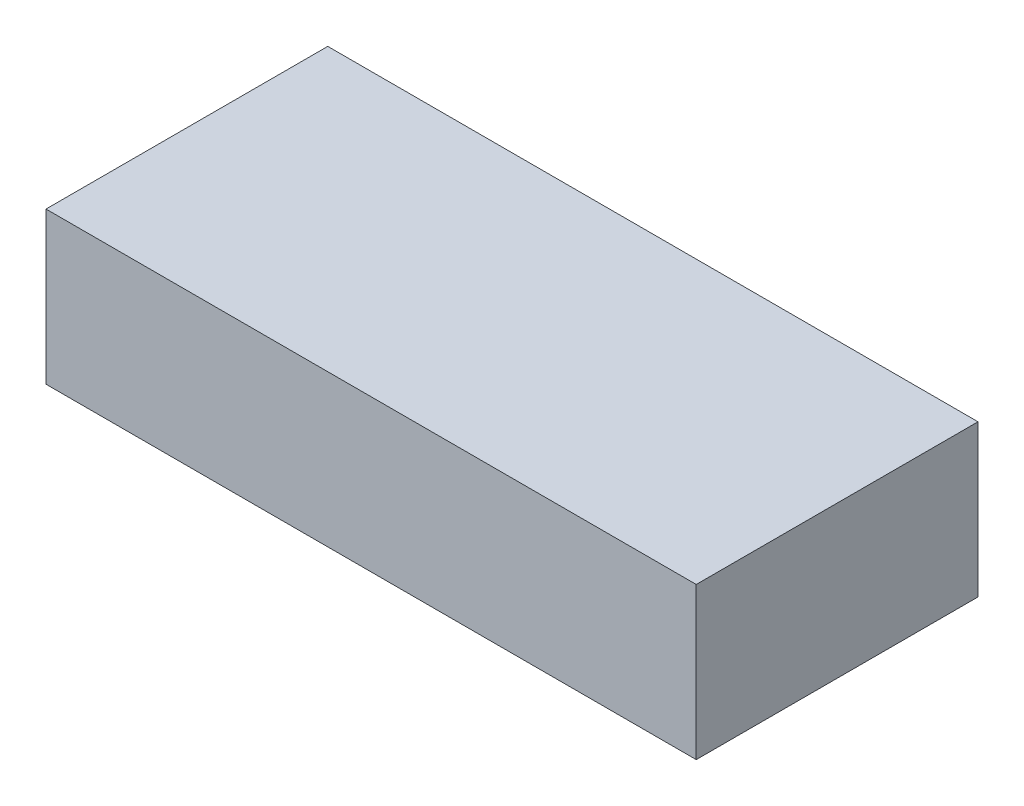
SolidWorks part; units mm, degrees
ref_plane "Front Plane" through (0, 0, 0) normal (0, 0, 1) x (1, 0, 0)
ref_plane "Top Plane" through (0, 0, 0) normal (0, 1, 0) x (1, 0, 0)
ref_plane "Right Plane" through (0, 0, 0) normal (1, 0, 0) x (0, 0, -1)
sketch "Sketch1" plane through (0, 0, 0) normal (0, 1, 0) x (1, 0, 0)
  line L1 (-75, -32.5) -> (75, -32.5)
  line L2 (-75, -32.5) -> (-75, 32.5)
  line L3 (-75, 32.5) -> (75, 32.5)
  line L4 (75, -32.5) -> (75, 32.5)
  line L5 (-75, -32.5) -> (75, 32.5) construction
  line L6 (-75, 32.5) -> (75, -32.5) construction
  point P0 (0, 0)
  dimension "D1" = 150
  dimension "D2" = 65
extrude "Boss-Extrude1" add sketch "Sketch1" along normal blind 35
sketch "Sketch2" plane through (0, 0, 0) normal (0, -1, 0) x (1, 0, 0)
  line L0 (-75, 32.5) -> (75, 32.5) construction
  line L1 (-71.952, -29.452) -> (71.952, -29.452)
  line L2 (-71.952, -29.452) -> (-71.952, 29.452)
  line L3 (-71.952, 29.452) -> (71.952, 29.452)
  line L4 (71.952, -29.452) -> (71.952, 29.452)
  line L5 (-71.952, -29.452) -> (71.952, 29.452) construction
  line L6 (-71.952, 29.452) -> (71.952, -29.452) construction
  line L7 (-75, -32.5) -> (-75, 32.5) construction
  point P0 (0, 0)
  dimension "D1" = 3.048
  dimension "D2" = 3.048
extrude "Cut-Extrude1" cut sketch "Sketch2" against normal blind 28.4
